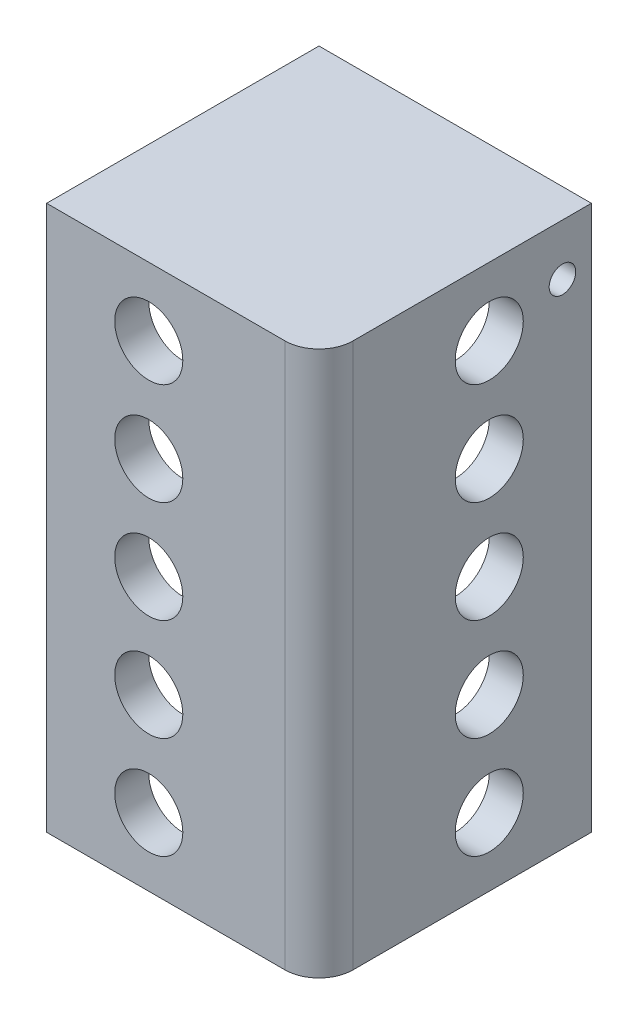
SolidWorks part; units mm, degrees
material "PET"
ref_plane "Front Plane" through (0, 0, 0) normal (0, 0, 1) x (1, 0, 0)
ref_plane "Top Plane" through (0, 0, 0) normal (0, 1, 0) x (1, 0, 0)
ref_plane "Right Plane" through (0, 0, 0) normal (1, 0, 0) x (0, 0, -1)
sketch "Sketch2" plane through (0, 0, 0) normal (0, 1, 0) x (1, 0, 0)
  line L1 (-41.3514, 76.4779) -> (60.2486, 76.4779)
  line L2 (-41.3514, 76.4779) -> (-41.3514, -25.1221)
  line L3 (-41.3514, -25.1221) -> (60.2486, -25.1221)
  line L4 (60.2486, 76.4779) -> (60.2486, -25.1221)
  dimension "D1" = 101.6
  dimension "D2" = 101.6
extrude "Boss-Extrude1" add sketch "Sketch2" along normal blind 203.2
ref_plane "Plane1" through (0, 101.6, 0) normal (0, 1, 0) x (1, 0, 0)
sketch "Sketch4" plane through (0, 101.6, 0) normal (0, 1, 0) x (1, 0, 0)
  line L0 (60.2486, -25.1221) -> (60.2486, 76.4779) construction
  line L1 (-41.3514, 76.4779) -> (47.5486, 76.4779)
  line L2 (-41.3514, 76.4779) -> (-41.3514, -12.4221)
  line L3 (-41.3514, -12.4221) -> (47.5486, -12.4221)
  line L4 (47.5486, 76.4779) -> (47.5486, -12.4221)
  line L5 (-41.3514, -25.1221) -> (60.2486, -25.1221) construction
  dimension "D1" = 12.7
  dimension "D2" = 12.7
extrude "Cut-Extrude1" cut sketch "Sketch4" along normal mid plane 190.5
fillet "Fillet1" radius 12.7 2 edges at (60.2486, 101.6, 25.1221) (47.5486, 101.6, 12.4221)
sketch "Sketch5" plane through (0, 0, 25.1221) normal (0, 0, 1) x (1, 0, 0)
  line L0 (-41.3514, 203.2) -> (47.5486, 203.2) construction
  line L1 (-41.3514, 0) -> (47.5486, 0) construction
  line L2 (-41.3514, 203.2) -> (-41.3514, 0) construction
  circle A0 centre (-3.2514, 177.8) radius 12.7
  circle A1 centre (-3.2514, 139.7) radius 12.7
  circle A2 centre (-3.2514, 101.6) radius 12.7
  circle A3 centre (-3.2514, 63.5) radius 12.7
  circle A4 centre (-3.2514, 25.4) radius 12.7
  dimension "D1" = 25.4
  dimension "D3" = 25.4
  dimension "D4" = 38.1
  dimension "D2" = 5
extrude "Cut-Extrude2" cut sketch "Sketch5" against normal through all
sketch "Sketch6" plane through (60.2486, 0, 0) normal (1, 0, 0) x (0, 0, -1)
  line L0 (-12.4221, 203.2) -> (76.4779, 203.2) construction
  line L1 (76.4779, 203.2) -> (76.4779, 0) construction
  circle A0 centre (38.3779, 177.8) radius 12.7
  circle A1 centre (38.3779, 139.7) radius 12.7
  circle A2 centre (38.3779, 101.6) radius 12.7
  circle A3 centre (38.3779, 63.5) radius 12.7
  circle A4 centre (38.3779, 25.4) radius 12.7
  dimension "D1" = 25.4
  dimension "D2" = 38.1
  dimension "D3" = 5
extrude "Cut-Extrude3" cut sketch "Sketch6" against normal through all
sketch "Sketch7" plane through (0, 6.35, 0) normal (0, 1, 0) x (1, 0, 0)
  line L0 (60.2486, -12.4221) -> (60.2486, 76.4779) construction
  line L1 (-41.3514, 76.4779) -> (47.5486, 76.4779)
  line L2 (-41.3514, 76.4779) -> (-41.3514, -12.4221)
  line L3 (-41.3514, -12.4221) -> (34.8486, -12.4221)
  line L4 (47.5486, 76.4779) -> (47.5486, 0.2779)
  line L5 (-41.3514, -25.1221) -> (47.5486, -25.1221) construction
  arc A0 (34.8486, -12.4221) -> (47.5486, 0.2779) centre (34.8486, 0.2779) ccw
  dimension "D3" = 12.7
  dimension "D1" = 12.7
  dimension "D2" = 12.7
extrude "Cut-Extrude4" cut sketch "Sketch7" against normal through all
sketch "Sketch31" plane through (0, 196.85, 0) normal (0, -1, 0) x (1, 0, 0)
  line L5 (47.5486, -76.4779) -> (-41.3514, -76.4779) construction
  line L10 (7.6706, -76.4779) -> (16.5606, -76.4779)
  line L16 (7.6706, -76.4779) -> (7.6706, -53.6179)
  line L17 (7.6706, -53.6179) -> (16.5606, -53.6179)
  line L18 (16.5606, -76.4779) -> (16.5606, -53.6179)
  line L19 (47.5486, -0.2779) -> (47.5486, -76.4779) construction
  line L20 (28.4986, -53.6179) -> (37.3886, -53.6179)
  line L21 (28.4986, -53.6179) -> (28.4986, -76.4779)
  line L22 (28.4986, -76.4779) -> (37.3886, -76.4779)
  line L23 (37.3886, -53.6179) -> (37.3886, -76.4779)
  dimension "D5" = 8.89
  dimension "D6" = 22.86
  dimension "D7" = 10.16
  dimension "D8" = 11.938
extrude "Boss-Extrude2" add sketch "Sketch31" along normal blind 25.4
fillet "Fillet2" radius 6.35 2 edges at (12.1156, 171.45, -53.6179) (32.9436, 171.45, -53.6179)
fillet "Fillet3" radius 12.7 2 edges at (32.9436, 171.45, -76.4779) (12.1156, 171.45, -76.4779)
sketch "Sketch32" plane through (7.6706, 0, 0) normal (-1, 0, 0) x (0, 0, 1)
  line L0 (-59.9679, 171.45) -> (-63.7779, 171.45) construction
  line L1 (-76.4779, 184.15) -> (-76.4779, 196.85) construction
  circle A0 centre (-65.6829, 184.023) radius 4.953
  dimension "D1" = 9.906
  dimension "D2" = 12.573
  dimension "D3" = 10.795
extrude "Cut-Extrude5" cut sketch "Sketch32" against normal through all
